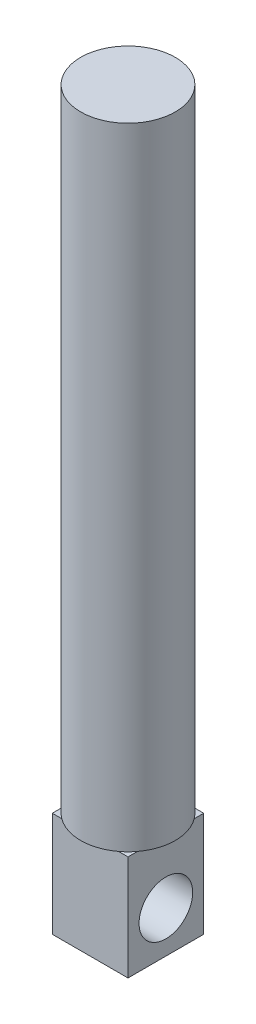
SolidWorks part; units mm, degrees
ref_plane "Front Plane" through (0, 0, 0) normal (0, 0, 1) x (1, 0, 0)
ref_plane "Top Plane" through (0, 0, 0) normal (0, 1, 0) x (1, 0, 0)
ref_plane "Right Plane" through (0, 0, 0) normal (1, 0, 0) x (0, 0, -1)
sketch "Sketch1" plane through (0, 0, 0) normal (0, 1, 0) x (1, 0, 0)
  line L1 (0, 0) -> (6, 0)
  line L2 (0, 0) -> (0, 6)
  line L3 (0, 6) -> (6, 6)
  line L4 (6, 0) -> (6, 6)
  dimension "D1" = 6
  dimension "D2" = 6
extrude "Boss-Extrude1" add sketch "Sketch1" along normal blind 8.31
sketch "Sketch2" plane through (6, 0, 0) normal (1, 0, 0) x (0, 0, -1)
  line L0 (0, 8.31) -> (6, 8.31) construction
  circle A0 centre (3, 3.31) radius 2.125
  dimension "D1" = 5
extrude "Cut-Extrude1" cut sketch "Sketch2" against normal blind 10
sketch "Sketch3" plane through (0, 8.31, 0) normal (0, 1, 0) x (1, 0, 0)
  line L0 (3, 0) -> (3, 6) construction
  line L1 (0, 0) -> (6, 0) construction
  line L2 (6, 6) -> (0, 6) construction
  line L3 (0, 3) -> (6, 3) construction
  line L4 (0, 6) -> (0, 0) construction
  line L5 (6, 0) -> (6, 6) construction
  circle A0 centre (3, 3) radius 3.75
extrude "Boss-Extrude2" add sketch "Sketch3" along normal blind 50
